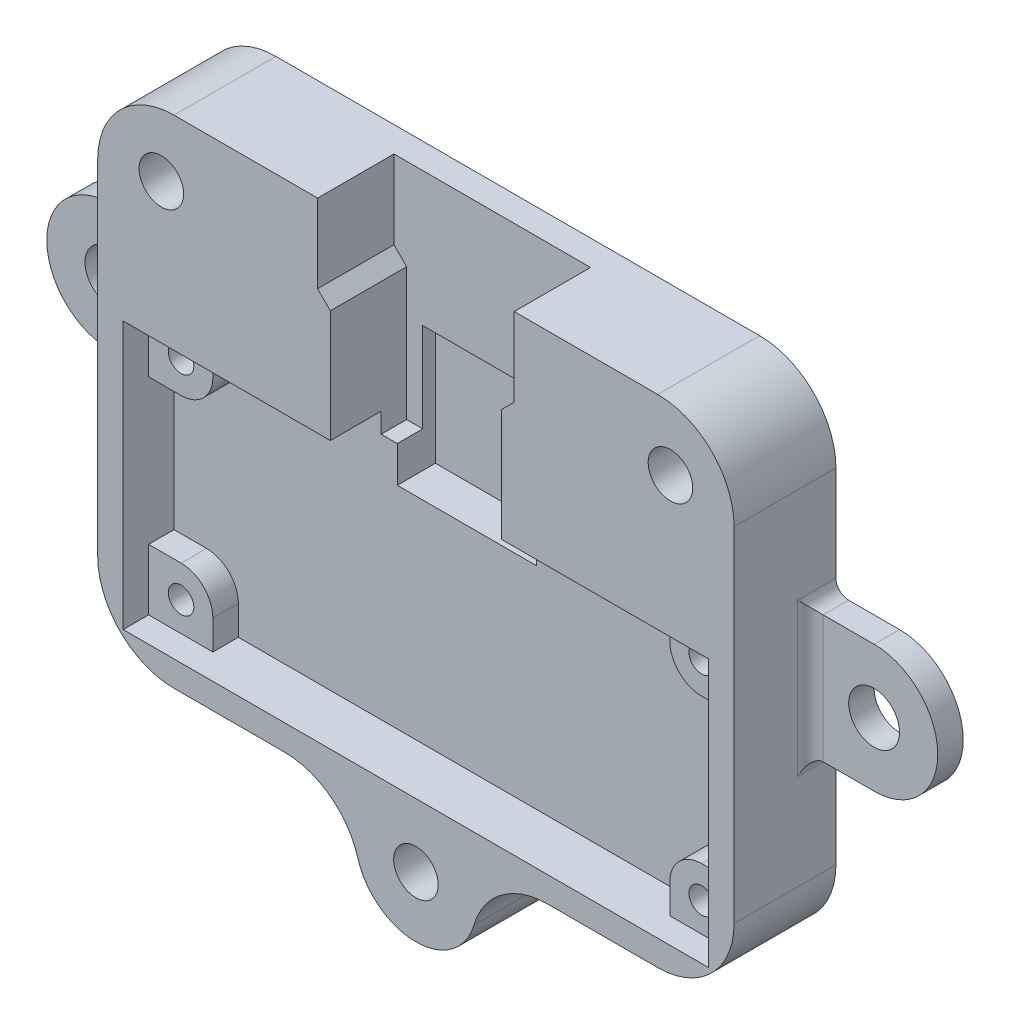
SolidWorks part; units mm, degrees
ref_plane "Front Plane" through (0, 0, 0) normal (0, 0, 1) x (1, 0, 0)
ref_plane "Top Plane" through (0, 0, 0) normal (0, 1, 0) x (1, 0, 0)
ref_plane "Right Plane" through (0, 0, 0) normal (1, 0, 0) x (0, 0, -1)
sketch "Sketch1" plane through (0, 0, 0) normal (0, 0, 1) x (1, 0, 0)
  line L0 (-4.75, -42) -> (-4.75, -39)
  line L1 (0, 0) -> (0, -58.1512) construction
  line L2 (25, 0) -> (-25, 0)
  line L3 (4.75, -42) -> (4.75, -39)
  line L6 (-25, 0) -> (-25, -39)
  line L7 (-25, -39) -> (-4.75, -39)
  line L8 (25, 0) -> (25, -39)
  line L15 (4.75, -39) -> (25, -39)
  circle A0 centre (-20, -5) radius 1.75
  circle A3 centre (20, -5) radius 1.75
  circle A5 centre (0, -42) radius 1.75
  arc A6 (-4.75, -42) -> (4.75, -42) centre (0, -42) ccw
  circle A8 centre (0, -42) radius 4.75 construction
  point P9 (0, -39)
  point P12 (0, 0)
  point P16 (6.5708, -17)
  point P20 (-14, -9.75)
  point P35 (3.25, -42)
  dimension "D5" = 3.5
  dimension "D9" = 3.5
  dimension "D4" = 5
  dimension "D2" = 5
  dimension "D3" = 50
  dimension "D10" = 3
  dimension "D11" = 3
extrude "Boss-Extrude1" add sketch "Sketch1" along normal blind 8
sketch "Sketch2" plane through (0, 0, 8) normal (0, 0, 1) x (1, 0, 0)
  line L2 (-25, 0) -> (-25, -39) construction
  line L3 (-23, -16) -> (23, -16)
  line L4 (-23, -16) -> (-23, -37)
  line L5 (-23, -37) -> (23, -37)
  line L6 (23, -16) -> (23, -37)
  line L7 (25, 0) -> (25, -39) construction
  line L8 (4.75, -39) -> (25, -39) construction
  dimension "D3" = 2
  dimension "D1" = 2
  dimension "D2" = 2
  dimension "D4" = 21
extrude "Cut-Extrude1" cut sketch "Sketch2" against normal blind 2
sketch "Sketch3" plane through (0, 0, 6) normal (0, 0, 1) x (1, 0, 0)
  line L0 (0, -16) -> (0, -37) construction
  line L3 (-17.95, -18.3) -> (-17.95, -16)
  line L4 (20.45, -34.7) -> (-20.45, -34.7) construction
  line L5 (20.45, -34.7) -> (20.45, -18.3) construction
  line L6 (20.45, -18.3) -> (-20.45, -18.3) construction
  line L7 (-20.45, -34.7) -> (-20.45, -18.3) construction
  line L8 (20.45, -34.7) -> (-20.45, -18.3) construction
  line L9 (20.45, -18.3) -> (-20.45, -34.7) construction
  line L11 (-20.45, -20.8) -> (-23, -20.8)
  line L15 (-23, -26.5) -> (20.45, -26.5) construction
  line L18 (20.45, -20.8) -> (23, -20.8)
  line L19 (17.95, -18.3) -> (17.95, -16)
  line L20 (17.95, -34.7) -> (17.95, -37)
  line L21 (20.45, -32.2) -> (23, -32.2)
  line L26 (-20.45, -32.2) -> (-23, -32.2)
  line L27 (-17.95, -34.7) -> (-17.95, -37)
  line L28 (-17.95, -16) -> (17.95, -16)
  line L29 (23, -20.8) -> (23, -32.2)
  line L30 (17.95, -37) -> (-17.95, -37)
  line L31 (-23, -32.2) -> (-23, -20.8)
  circle A0 centre (-20.45, -18.3) radius 1
  arc A1 (-20.45, -20.8) -> (-17.95, -18.3) centre (-20.45, -18.3) ccw
  arc A2 (20.45, -20.8) -> (17.95, -18.3) centre (20.45, -18.3) cw
  circle A3 centre (-20.45, -18.3) radius 2.5 construction
  circle A4 centre (20.45, -18.3) radius 1
  circle A5 centre (20.45, -34.7) radius 1
  arc A6 (20.45, -32.2) -> (17.95, -34.7) centre (20.45, -34.7) ccw
  arc A7 (-20.45, -32.2) -> (-17.95, -34.7) centre (-20.45, -34.7) cw
  circle A8 centre (-20.45, -34.7) radius 1
  point P6 (0, -26.5)
  point P22 (-17.9, -18.3)
  dimension "D3" = 2
  dimension "D1" = 16.4
  dimension "D2" = 40.9
  dimension "D4" = 1.5
extrude "Cut-Extrude2" cut sketch "Sketch3" against normal blind 2
sketch "Sketch4" plane through (0, 0, 8) normal (0, 0, 1) x (1, 0, 0)
  line L0 (-7.723, 0) -> (-7.723, -6.1725)
  line L1 (25, 0) -> (-25, 0) construction
  line L2 (-7.723, -6.1725) -> (-6.723, -7.1725)
  line L3 (-6.723, -7.1725) -> (-6.723, -17.5725)
  line L4 (-6.723, -17.5725) -> (6.723, -17.5725)
  line L5 (7.723, 0) -> (-7.723, 0)
  line L6 (0, 0) -> (0, -17.5725) construction
  line L7 (-7.223, 2.8275) -> (-7.223, -5.1725) construction
  line L8 (-6.223, -6.1725) -> (-6.223, -16.5725) construction
  line L9 (-6.223, -16.5725) -> (6.223, -16.5725) construction
  line L10 (6.723, -7.1725) -> (6.723, -17.5725)
  line L11 (7.723, -6.1725) -> (6.723, -7.1725)
  line L12 (7.723, 0) -> (7.723, -6.1725)
  dimension "D1" = 0.5
  dimension "D2" = 0.5
  dimension "D3" = 1
  dimension "D4" = 135
  dimension "D5" = 1
extrude "Cut-Extrude3" cut sketch "Sketch4" against normal blind 6 contours L0 L2 L3 L4 L10 L11 L12 L5
sketch "Sketch5" plane through (0, 0, 8) normal (0, 0, 1) x (1, 0, 0)
  line L0 (0, 0) -> (0, -46.75) construction
  line L1 (7.723, 0) -> (-7.723, 0) construction
  line L3 (5.4638, -10.5445) -> (-5.4638, -10.5445)
  line L4 (5.4638, -10.5445) -> (5.4638, -20.415)
  line L5 (5.4638, -20.415) -> (-5.4638, -20.415)
  line L6 (-5.4638, -10.5445) -> (-5.4638, -20.415)
  line L7 (5.4638, -10.5445) -> (-5.4638, -20.415) construction
  line L8 (5.4638, -20.415) -> (-5.4638, -10.5445) construction
  arc A0 (-4.75, -42) -> (4.75, -42) centre (0, -42) ccw construction
  point P7 (0, -15.4797)
extrude "Cut-Extrude4" cut sketch "Sketch5" against normal blind 7
fillet "Fillet4" radius 6 6 edges at (25, -39, 4) (4.75, -39, 4) (-25, -39, 4) (-4.75, -39, 4) (25, 0, 4) (-25, 0, 4)
chamfer "Chamfer2" distance 1 angle 45 3 edges at (1.75, -42, 0) (-18.25, -5, 0) (21.75, -5, 0)
sketch "Sketch7" plane through (0, 0, 0) normal (0, 0, -1) x (-1, 0, 0)
  line L0 (-25, -19.5) -> (25, -19.5) construction
  line L1 (-25, -6) -> (-25, -33) construction
  line L2 (25, -6) -> (25, -33) construction
  line L3 (-30, -14.5) -> (-25, -14.5)
  line L4 (-30, -24.5) -> (-25, -24.5)
  line L5 (-25, -14.5) -> (-25, -24.5)
  line L6 (0, -46.75) -> (0, 0) construction
  line L7 (-19, 0) -> (19, 0) construction
  line L8 (25, -14.5) -> (25, -24.5)
  line L9 (30, -24.5) -> (25, -24.5)
  line L10 (30, -14.5) -> (25, -14.5)
  circle A0 centre (-30, -19.5) radius 2
  arc A1 (-30, -14.5) -> (-30, -24.5) centre (-30, -19.5) ccw
  arc A2 (-4.5613, -43.3256) -> (4.5613, -43.3256) centre (0, -42) ccw construction
  circle A3 centre (-30, -19.5) radius 5 construction
  circle A4 centre (30, -19.5) radius 2
  arc A5 (30, -14.5) -> (30, -24.5) centre (30, -19.5) cw
  point P14 (-25, -26.5)
  line M18 (-25, -6) -> (-25, -33)
  line M28 (25, -33) -> (25, -6)
  dimension "D1" = 4
  dimension "D3" = 5
  dimension "D2" = 5
extrude "Boss-Extrude2" add sketch "Sketch7" against normal blind 2 contours L3 A1 L4 A0 M18 | A5 L10 L9 A4 M28
fillet "Fillet5" radius 1 6 edges at (25, -19.5, 2) (-25, -19.5, 2) (-25, -14.5, 1) (-25, -24.5, 1) (25, -14.5, 1) (25, -24.5, 1)
